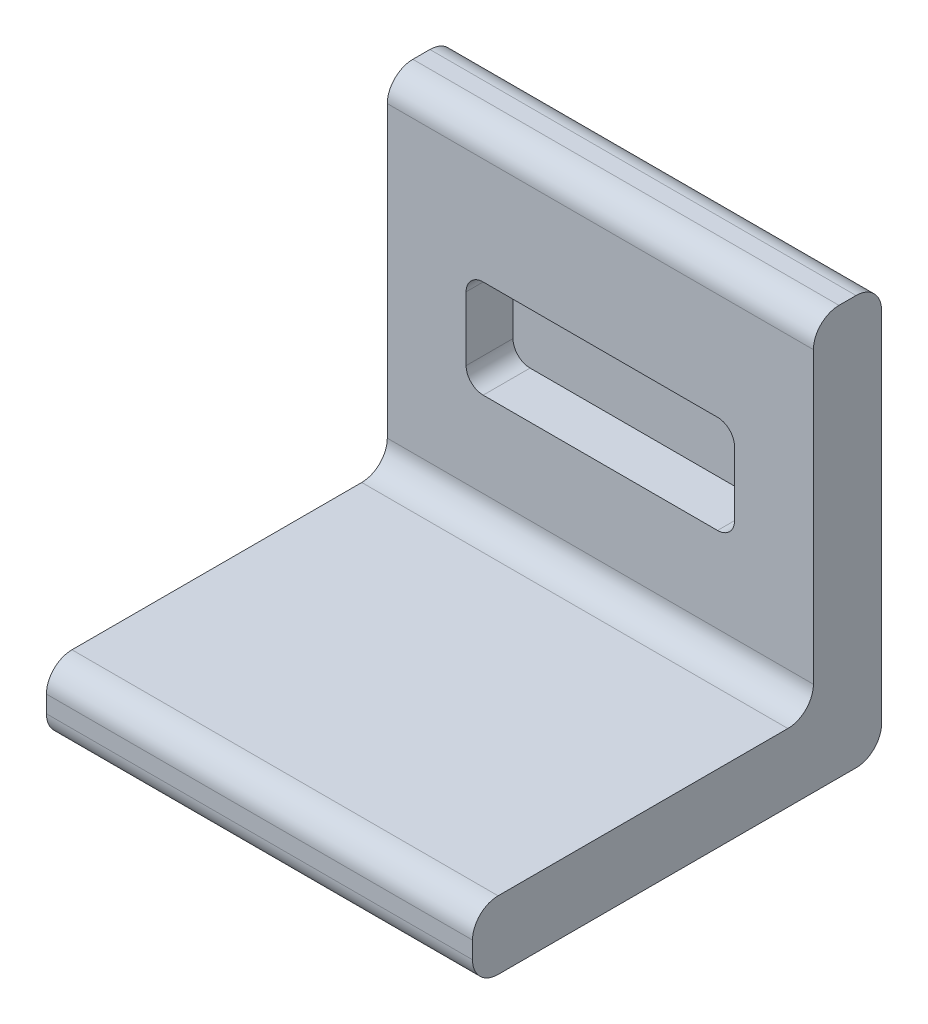
SolidWorks part; units mm, degrees
ref_plane "Front Plane" through (0, 0, 0) normal (0, 0, 1) x (1, 0, 0)
ref_plane "Top Plane" through (0, 0, 0) normal (0, 1, 0) x (1, 0, 0)
ref_plane "Right Plane" through (0, 0, 0) normal (1, 0, 0) x (0, 0, -1)
sketch "Sketch1" plane through (0, 0, 0) normal (0, 1, 0) x (1, 0, 0)
  line L0 (0, 0) -> (0, 46.6895) construction
  line L1 (-25, 40) -> (25, 40)
  line L2 (-25, 40) -> (-25, 0)
  line L3 (-25, 0) -> (25, 0)
  line L4 (25, 40) -> (25, 0)
  dimension "D1" = 50
  dimension "D2" = 40
extrude "Boss-Extrude1" add sketch "Sketch1" along normal blind 8
sketch "Sketch2" plane through (0, 0, -40) normal (0, 0, -1) x (-1, 0, 0)
  line L0 (-25, 8) -> (-25, 0) construction
  line L1 (-25, 48) -> (25, 48)
  line L2 (-25, 48) -> (-25, 0)
  line L3 (-25, 0) -> (25, 0)
  line L4 (25, 48) -> (25, 0)
  line L5 (25, 8) -> (25, 0) construction
  line L6 (-25, 8) -> (25, 8) construction
  dimension "D1" = 40
extrude "Boss-Extrude2" add sketch "Sketch2" along normal blind 8
sketch "Sketch3" plane through (0, 0, -40) normal (0, 0, 1) x (1, 0, 0)
  line L0 (0, 0) -> (0, 36.9321) construction
  line L1 (-15.75, 32.5) -> (15.75, 32.5)
  line L2 (-15.75, 32.5) -> (-15.75, 21)
  line L3 (-15.75, 21) -> (15.75, 21)
  line L4 (15.75, 32.5) -> (15.75, 21)
  line L5 (25, 8) -> (-25, 8) construction
  dimension "D1" = 13
  dimension "D2" = 31.5
  dimension "D3" = 11.5
extrude "Cut-Extrude1" cut sketch "Sketch3" against normal blind 5.5
fillet "Fillet1" radius 2 4 edges at (15.75, 21, -42.75) (15.75, 32.5, -42.75) (-15.75, 32.5, -42.75) (-15.75, 21, -42.75)
fillet "Fillet2" radius 3 6 edges at (0, 48, -48) (0, 0, 0) (0, 0, -48) (0, 8, -40) (0, 8, 0) (0, 48, -40)
